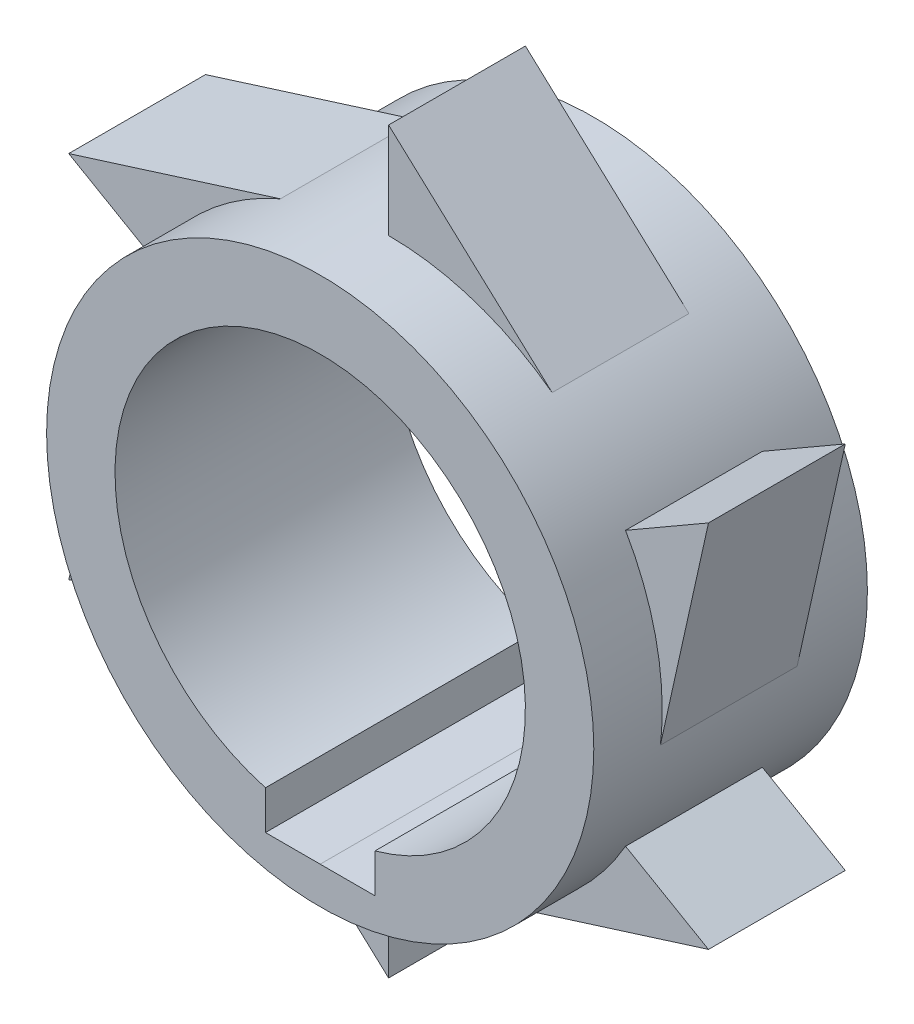
SolidWorks part; units mm, degrees
ref_plane "Front Plane" through (0, 0, 0) normal (0, 0, 1) x (1, 0, 0)
ref_plane "Top Plane" through (0, 0, 0) normal (0, 1, 0) x (1, 0, 0)
ref_plane "Right Plane" through (0, 0, 0) normal (1, 0, 0) x (0, 0, -1)
sketch "Sketch1" plane through (0, 0, 0) normal (0, 0, 1) x (1, 0, 0)
  circle A0 centre (0, 0) radius 15
  circle A1 centre (0, 0) radius 20
extrude "Boss-Extrude1" add sketch "Sketch1" along normal blind 20 contours A1 | A0
ref_plane "Plane1" through (0, 0, 5) normal (0, 0, 1) x (1, 0, 0)
sketch "Sketch5" plane through (0, 0, 0) normal (0, 0, 1) x (1, 0, 0)
  line L0 (0, 0.5432) -> (0, 0) construction
  line L1 (0, 0) -> (0, -17.2933) construction
  line L2 (0, -17.2933) -> (-4, -17.2933)
  line L3 (-4, -17.2933) -> (-4, -14.4568)
  line L4 (0, -17.2933) -> (4, -17.2933)
  line L5 (4, -17.2933) -> (4, -14.4568)
  circle A0 centre (0, 0) radius 15 construction
extrude "Cut-Extrude2" cut sketch "Sketch5" against normal through all and the other way through all
sketch "Sketch18" plane through (0, 0, 5) normal (0, 0, 1) x (1, 0, 0)
  line L0 (0, 20) -> (0, 27)
  line L1 (0, 27) -> (14.9472, 13.2884)
  circle A0 centre (0, 0) radius 20 construction
  circle A2 centre (0, 0) radius 20
  arc A3 (14.9472, 13.2884) -> (0, 20) centre (0, 0) ccw
  dimension "D1" = 0
extrude "Boss-Extrude16" add sketch "Sketch18" along normal blind 10 contours A3 L1 L0
pattern_circular "CirPattern2" count 6 over 360 about axis through (0, 0, 0) along (0, 0, 1) of "Boss-Extrude16"
